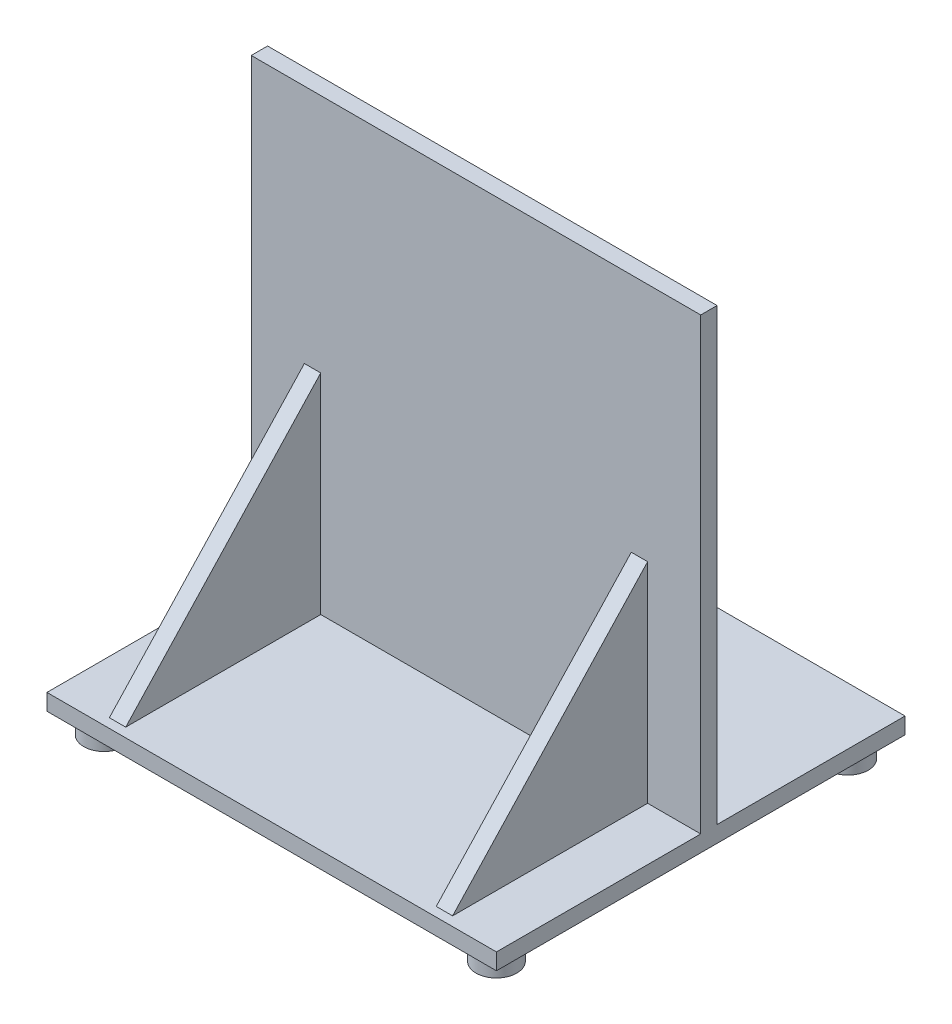
SolidWorks part; units mm, degrees
ref_plane "Plan de face" through (0, 0, 0) normal (0, 0, 1) x (1, 0, 0)
ref_plane "Plan de dessus" through (0, 0, 0) normal (0, 1, 0) x (1, 0, 0)
ref_plane "Plan de droite" through (0, 0, 0) normal (1, 0, 0) x (0, 0, -1)
sketch "Esquisse1" plane through (0, 0, 0) normal (0, 0, 1) x (1, 0, 0)
  line L0 (0, -55) -> (0, 55) construction
  line L1 (0, 82.7885) -> (110, 82.7885)
  line L2 (0, 82.7885) -> (0, -27.2115)
  line L3 (0, -27.2115) -> (110, -27.2115)
  line L4 (110, 82.7885) -> (110, -27.2115)
  dimension "D1" = 110
  dimension "D2" = 110
  dimension "D3" = 0
extrude "Boss.-Extru.1" add sketch "Esquisse1" along normal blind 4
sketch "Esquisse2" plane through (0, -27.2115, 0) normal (0, -1, 0) x (1, 0, 0)
  line L5 (0, 4) -> (110, 4) construction
  line L6 (0, -46) -> (110, -46)
  line L7 (0, -46) -> (0, 54)
  line L8 (0, 54) -> (110, 54)
  line L9 (110, -46) -> (110, 54)
  line L10 (0, 4) -> (0, 0) construction
  dimension "D1" = 100
  dimension "D2" = 50
  dimension "D3" = 110
  dimension "D4" = 0
extrude "Boss.-Extru.2" add sketch "Esquisse2" along normal blind 4
sketch "Esquisse3" plane through (0, 0, 0) normal (0, 0, -1) x (-1, 0, 0)
  line L0 (-110, -27.2115) -> (-110, 82.7885) construction
  line L1 (-105, 77.7885) -> (-5, 77.7885)
  line L2 (-105, 77.7885) -> (-105, -22.2115)
  line L3 (-105, -22.2115) -> (-5, -22.2115)
  line L4 (-5, 77.7885) -> (-5, -22.2115)
  line L7 (-110, 82.7885) -> (0, 82.7885) construction
  dimension "D1" = 100
  dimension "D2" = 100
  dimension "D3" = 5
  dimension "D4" = 5
extrude "Enlèv. mat.-Extru.1" cut sketch "Esquisse3" against normal blind 1
sketch "Esquisse6" plane through (0, -31.2115, 0) normal (0, -1, 0) x (1, 0, 0)
  line L4 (0, -46) -> (110, -46) construction
  line L5 (110, -46) -> (110, 54) construction
  line L6 (0, 54) -> (0, -46) construction
  line L7 (110, 54) -> (0, 54) construction
  circle A0 centre (7, 47) radius 5
  circle A1 centre (103, 47) radius 5
  circle A2 centre (7, -39) radius 5
  circle A3 centre (103, -39) radius 5
  point P8 (0, 0)
  dimension "D1" = 10
  dimension "D4" = 10
  dimension "D7" = 10
  dimension "D8" = 10
  dimension "D2" = 7
  dimension "D3" = 7
  dimension "D5" = 7
  dimension "D6" = 7
  dimension "D9" = 7
  dimension "D10" = 7
  dimension "D11" = 7
  dimension "D12" = 7
  dimension "D13" = 86
  dimension "D14" = 96
extrude "Boss.-Extru.3" add sketch "Esquisse6" along normal blind 5
ref_plane "Plan1" through (15, 0, 0) normal (1, 0, 0) x (0, 0, -1)
ref_plane "Plan2" through (95, 0, 0) normal (1, 0, 0) x (0, 0, -1)
sketch "Esquisse8" plane through (15, 0, 0) normal (1, 0, 0) x (0, 0, -1)
  line L0 (-51.726, -27.2115) -> (-4, 23.9962)
  line L1 (-74, -27.2115) -> (-4, -27.2115) construction
  line L2 (-4, 82.7885) -> (-4, -27.2115) construction
  point P2 (-51.726, -27.2115)
  point P5 (-4, 33.3808)
rib "Nervure1" sketch "Esquisse8" sketch "Esquisse8" thickness 4 extrusion direction parallel to sketch draft on no parameters "D1"=4
sketch "Esquisse11" plane through (0, 0, 4) normal (0, 0, 1) x (1, 0, 0)
  line L0 (13, 23.9962) -> (110, 23.9962)
  line L1 (110, -27.2115) -> (110, 82.7885) construction
sketch "Esquisse12" plane through (0, -27.2115, 0) normal (0, 1, 0) x (1, 0, 0)
  line L0 (13, -51.726) -> (111.0251, -51.726)
sketch "Esquisse9" plane through (95, 0, 0) normal (1, 0, 0) x (0, 0, -1)
  line L0 (-4, 23.9962) -> (-51.726, -27.2115)
  line L1 (-4, -27.2115) -> (-74, -27.2115) construction
  line L2 (-4, -27.2115) -> (-51.726, -27.2115) construction
  line L3 (-4, -27.2115) -> (-4, 82.7885) construction
  line L4 (-4, -27.2115) -> (-4, 23.9962) construction
  point P6 (-18.2962, -22.3585)
  point P7 (-4, 23.9962)
rib "Nervure6" sketch "Esquisse9" sketch "Esquisse9" thickness 4 extrusion direction parallel to sketch draft on no parameters "D1"=4
